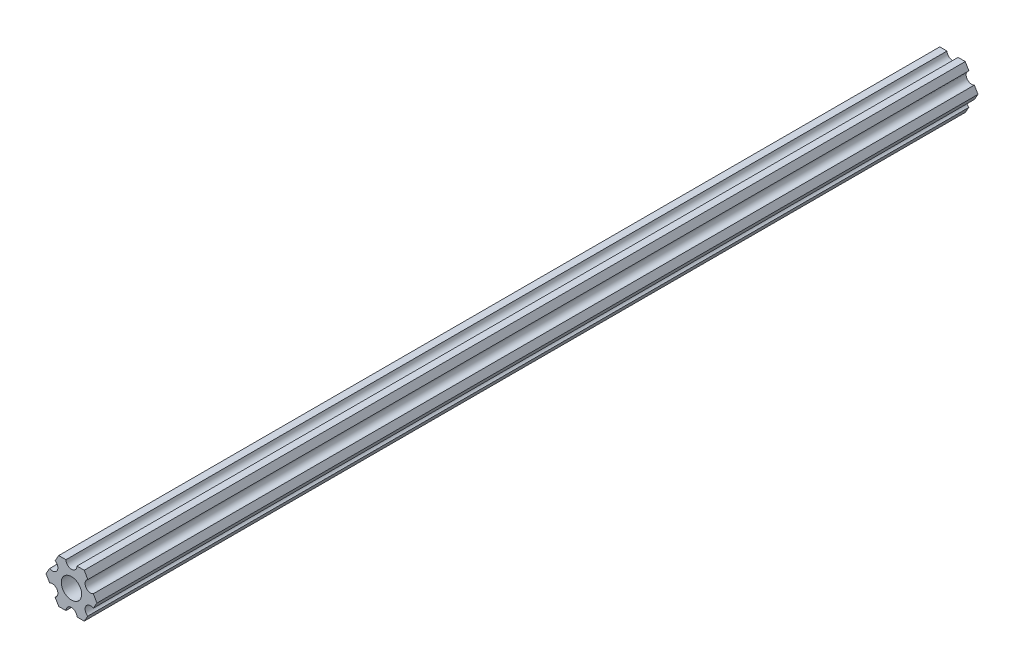
SolidWorks part; units mm, degrees
material "6061 Alloy"
ref_plane "Front Plane" through (0, 0, 0) normal (0, 0, 1) x (1, 0, 0)
ref_plane "Top Plane" through (0, 0, 0) normal (0, 1, 0) x (1, 0, 0)
ref_plane "Right Plane" through (0, 0, 0) normal (1, 0, 0) x (0, 0, -1)
ref_plane "Plane1" through (0, 0, 0) normal (0, 0, -1) x (-1, 0, 0)
sketch "Sketch1" plane through (0, 0, 0) normal (0, 0, -1) x (-1, 0, 0)
  line L0 (-4.7055, -4.5498) -> (-3.6662, -6.35)
  line L1 (-3.6662, -6.35) -> (-1.5875, -6.35)
  line L2 (1.5875, -6.35) -> (3.6662, -6.35)
  line L3 (3.6662, -6.35) -> (4.7055, -4.5498)
  line L4 (6.293, -1.8002) -> (7.3323, 0)
  line L5 (7.3323, 0) -> (6.293, 1.8002)
  line L6 (4.7055, 4.5498) -> (3.6662, 6.35)
  line L7 (3.6662, 6.35) -> (1.5875, 6.35)
  line L8 (-1.5875, 6.35) -> (-3.6662, 6.35)
  line L9 (-3.6662, 6.35) -> (-4.7055, 4.5498)
  line L10 (-6.293, 1.8002) -> (-7.3323, 0)
  line L11 (-7.3323, 0) -> (-6.293, -1.8002)
  circle A0 centre (0, 0) radius 2.9337
  arc A1 (-6.293, -1.8002) -> (-4.7055, -4.5498) centre (-5.4993, -3.175) cw
  arc A2 (-1.5875, -6.35) -> (1.5875, -6.35) centre (0, -6.35) cw
  arc A3 (4.7055, -4.5498) -> (6.293, -1.8002) centre (5.4993, -3.175) cw
  arc A4 (6.293, 1.8002) -> (4.7055, 4.5498) centre (5.4993, 3.175) cw
  arc A5 (1.5875, 6.35) -> (-1.5875, 6.35) centre (0, 6.35) cw
  arc A6 (-4.7055, 4.5498) -> (-6.293, 1.8002) centre (-5.4993, 3.175) cw
  dimension "D1" = 5.8674
  dimension "D2" = 1.5875
  dimension "D3" = 5.4993
  dimension "D4" = 6.293
extrude "Boss-Extrude1" add sketch "Sketch1" against normal blind 253.619
